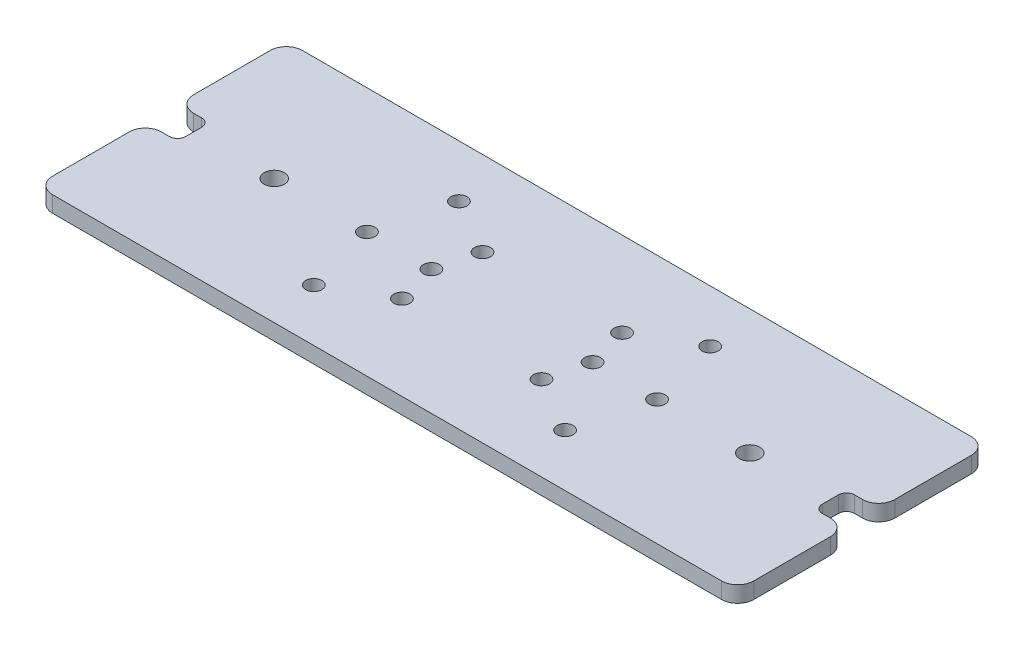
SolidWorks part; units mm, degrees
material "Acrylic (Medium-high impact)"
ref_plane "Front Plane" through (0, 0, 0) normal (0, 0, 1) x (1, 0, 0)
ref_plane "Top Plane" through (0, 0, 0) normal (0, 1, 0) x (1, 0, 0)
ref_plane "Right Plane" through (0, 0, 0) normal (1, 0, 0) x (0, 0, -1)
sketch "Sketch1" plane through (0, 0, 0) normal (0, 1, 0) x (1, 0, 0)
  line L1 (138.1125, 49.2125) -> (-138.1125, 49.2125)
  line L2 (138.1125, 49.2125) -> (138.1125, -49.2125)
  line L3 (138.1125, -49.2125) -> (-138.1125, -49.2125)
  line L4 (-138.1125, 49.2125) -> (-138.1125, -49.2125)
  line L5 (138.1125, 49.2125) -> (-138.1125, -49.2125) construction
  line L6 (138.1125, -49.2125) -> (-138.1125, 49.2125) construction
  point P0 (0, 0)
  dimension "D1" = 98.425
  dimension "D2" = 276.225
extrude "Boss-Extrude1" add sketch "Sketch1" along normal blind 6.35
sketch "Sketch2" plane through (0, 6.35, 0) normal (0, 1, 0) x (1, 0, 0)
  line L0 (93.6625, 0) -> (-93.6625, 0)
  line L1 (-138.1125, 49.2125) -> (-138.1125, -49.2125) construction
  point P4 (0, 0)
  dimension "D1" = 44.45
hole_wizard "5/16 (0.332) Dowel Hole1" positions "Sketch3" profile "Sketch4" hole size "5/16" standard "ANSI Inch" end condition up to next
sketch "Sketch3" plane through (0, 6.35, 0) normal (0, 1, 0) x (1, 0, 0)
  point P0 (-93.6625, 0)
  point P3 (93.6625, 0)
sketch "Sketch4" plane through (-93.6625, 6.35, 0) normal (1, 0, 0) x (0, 0, 1)
  line L0 (0, 0) -> (0, 6.35)
  line L1 (0, 6.35) -> (3.9687, 6.35)
  line L2 (3.9687, 6.35) -> (3.9687, 0)
  line L5 (3.9687, 0) -> (0, 0)
  line L11 (0, -6.35) -> (0, 107.95) construction
  dimension "Thru Hole Dia." = 7.9375
  dimension "Thru Hole Depth" = 6.35
sketch "Sketch5" plane through (0, 6.35, 0) normal (0, 1, 0) x (1, 0, 0)
  line L0 (-138.1125, 49.2125) -> (-138.1125, -49.2125) construction
  line L1 (-138.1125, 6.35) -> (-125.4125, 6.35)
  line L2 (-138.1125, 6.35) -> (-138.1125, -6.35)
  line L3 (-138.1125, -6.35) -> (-125.4125, -6.35)
  line L4 (-125.4125, 6.35) -> (-125.4125, -6.35)
  line L5 (138.1125, -49.2125) -> (138.1125, 49.2125) construction
  line L6 (138.1125, 6.35) -> (125.4125, 6.35)
  line L7 (138.1125, 6.35) -> (138.1125, -6.35)
  line L8 (138.1125, -6.35) -> (125.4125, -6.35)
  line L9 (125.4125, 6.35) -> (125.4125, -6.35)
  line L10 (93.6625, 0) -> (-93.6625, 0) construction
  point P12 (-125.4125, 0)
  point P15 (125.4125, 0)
  dimension "D1" = 12.7
extrude "Cut-Extrude1" cut sketch "Sketch5" against normal through all
fillet "Fillet1" radius 3.175 4 edges at (125.4125, 3.175, -6.35) (125.4125, 3.175, 6.35) (-125.4125, 3.175, 6.35) (-125.4125, 3.175, -6.35)
fillet "Fillet2" radius 6.35 8 edges at (-138.1125, 3.175, 6.35) (-138.1125, 3.175, 49.2125) (138.1125, 3.175, 49.2125) (138.1125, 3.175, 6.35) (138.1125, 3.175, -6.35) (138.1125, 3.175, -49.2125) (-138.1125, 3.175, -6.35) (-138.1125, 3.175, -49.2125)
sketch "Sketch6" plane through (0, 6.35, 0) normal (0, 1, 0) x (1, 0, 0)
  line L0 (93.6625, 0) -> (-93.6625, 0) construction
  line L1 (-57.15, 0) -> (-31.75, 0) construction
  line L2 (31.75, 0) -> (57.15, 0) construction
  circle A0 centre (0, 0) radius 44.45 construction
  point P3 (57.15, 0)
  point P4 (-57.15, 0)
  point P7 (-31.75, 0)
  point P8 (31.75, 0)
  point P11 (-44.45, 0)
  point P14 (44.45, 0)
  point P15 (49.4934, 28.575)
  point P18 (49.4934, -28.575)
  point P19 (-49.4934, 28.575)
  point P20 (-27.4963, 15.875)
  point P21 (27.4963, -15.875)
  point P22 (0, 0)
  point P23 (-49.4934, -28.575)
  point P24 (-27.4963, -15.875)
  point P25 (27.4963, 15.875)
  point P26 (0, 0)
  dimension "D1" = 88.9
  dimension "D2" = 25.4
  dimension "D3" = 2
  dimension "D4" = 2
hole_wizard "1/4 (0.2500) Dowel Hole1" positions "Sketch7" profile "Sketch8" hole size "1/4" standard "ANSI Inch" end condition up to next
sketch "Sketch7" plane through (0, 6.35, 0) normal (0, 1, 0) x (1, 0, 0)
  point P0 (-57.15, 0)
  point P3 (-31.75, 0)
  point P6 (31.75, 0)
  point P9 (57.15, 0)
  point P13 (-49.4934, 28.575)
  point P16 (-27.4963, 15.875)
  point P19 (-27.4963, -15.875)
  point P22 (-49.4934, -28.575)
  point P25 (27.4963, 15.875)
  point P28 (49.4934, 28.575)
  point P31 (49.4934, -28.575)
  point P34 (27.4963, -15.875)
sketch "Sketch8" plane through (-57.15, 6.35, 0) normal (1, 0, 0) x (0, 0, 1)
  line L0 (0, 0) -> (0, 6.35)
  line L1 (0, 6.35) -> (3.175, 6.35)
  line L2 (3.175, 6.35) -> (3.175, 0)
  line L5 (3.175, 0) -> (0, 0)
  line L11 (0, -6.35) -> (0, 107.95) construction
  dimension "Thru Hole Dia." = 6.35
  dimension "Thru Hole Depth" = 6.35
